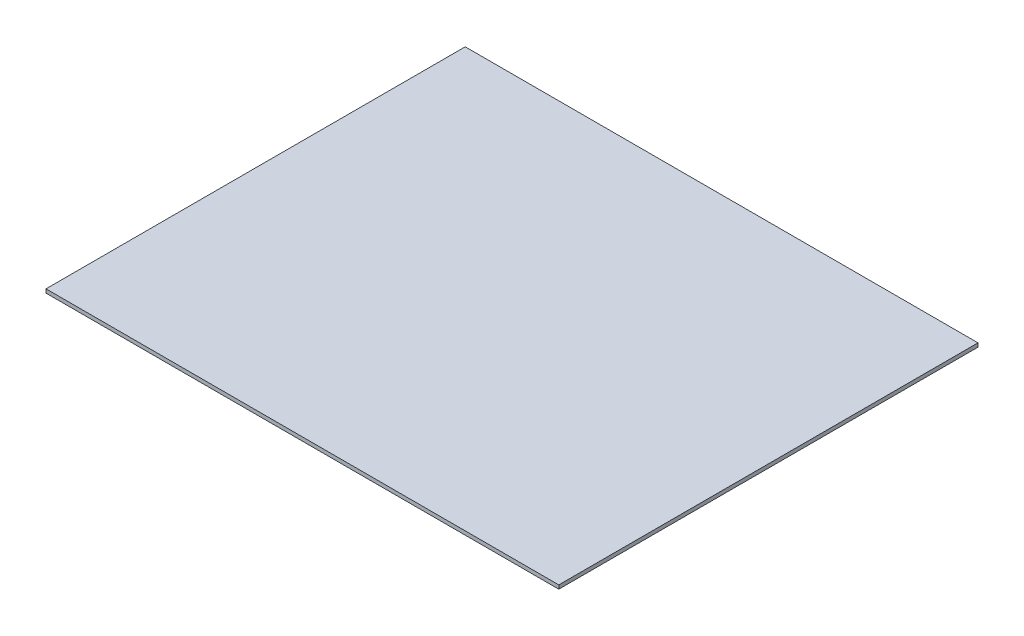
SolidWorks part; units mm, degrees
ref_plane "Front Plane" through (0, 0, 0) normal (0, 0, 1) x (1, 0, 0)
ref_plane "Top Plane" through (0, 0, 0) normal (0, 1, 0) x (1, 0, 0)
ref_plane "Right Plane" through (0, 0, 0) normal (1, 0, 0) x (0, 0, -1)
sketch "Sketch1" plane through (0, 0, 0) normal (0, 1, 0) x (1, 0, 0)
  line L1 (-217.4875, -177.8) -> (217.4875, -177.8)
  line L2 (-217.4875, -177.8) -> (-217.4875, 177.8)
  line L3 (-217.4875, 177.8) -> (217.4875, 177.8)
  line L4 (217.4875, -177.8) -> (217.4875, 177.8)
  line L5 (-217.4875, -177.8) -> (217.4875, 177.8) construction
  line L6 (-217.4875, 177.8) -> (217.4875, -177.8) construction
  point P0 (0, 0)
  dimension "D1" = 434.975
  dimension "D2" = 355.6
extrude "Boss-Extrude1" add sketch "Sketch1" against normal blind 3.175
